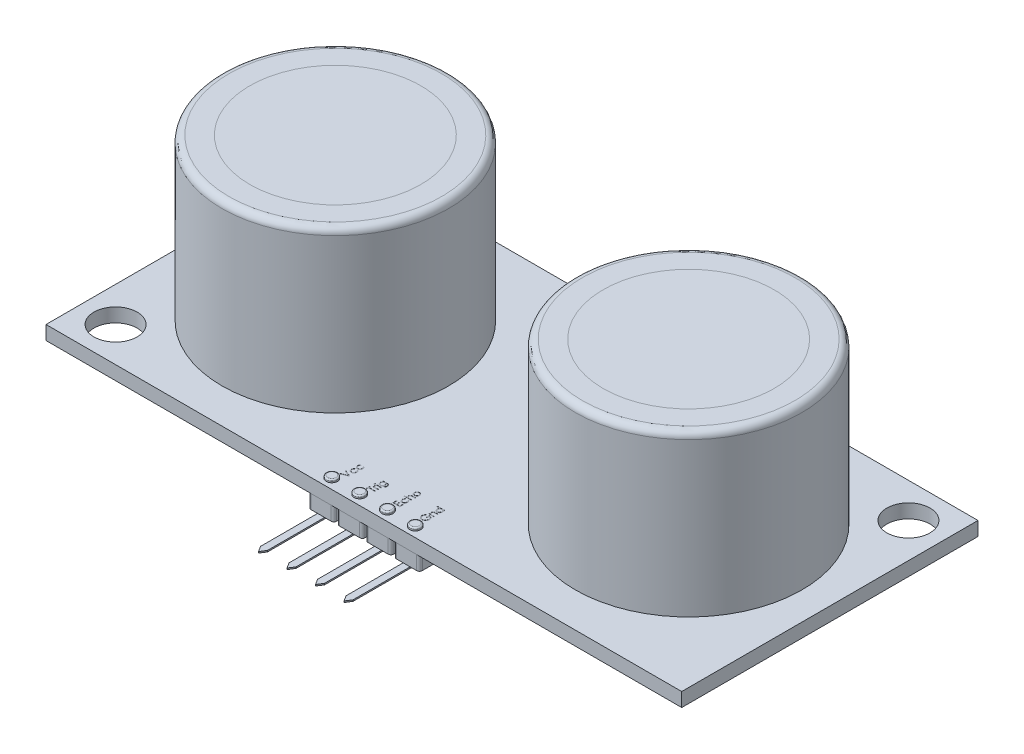
SolidWorks part; units mm, degrees
ref_plane "Front Plane" through (0, 0, 0) normal (0, 0, 1) x (1, 0, 0)
ref_plane "Top Plane" through (0, 0, 0) normal (0, 1, 0) x (1, 0, 0)
ref_plane "Right Plane" through (0, 0, 0) normal (1, 0, 0) x (0, 0, -1)
sketch "Sketch1" plane through (0, 0, 0) normal (0, 1, 0) x (1, 0, 0)
  line L1 (22.85, -10.65) -> (-22.85, -10.65)
  line L2 (22.85, -10.65) -> (22.85, 10.65)
  line L3 (22.85, 10.65) -> (-22.85, 10.65)
  line L4 (-22.85, -10.65) -> (-22.85, 10.65)
  line L5 (22.85, -10.65) -> (-22.85, 10.65) construction
  line L6 (22.85, 10.65) -> (-22.85, -10.65) construction
  circle A0 centre (20.35, 8.15) radius 1.55
  circle A1 centre (-20.35, -8.15) radius 1.55
  point P0 (0, 0)
  dimension "D3" = 3.1
  dimension "D1" = 45.7
  dimension "D2" = 21.3
  dimension "D4" = 2.5
  dimension "D5" = 2.5
  dimension "D6" = 2.5
  dimension "D7" = 2.5
extrude "Boss-Extrude1" add sketch "Sketch1" along normal blind 1
sketch "Sketch2" plane through (0, 1, 0) normal (0, 1, 0) x (1, 0, 0)
  line L0 (0, 0) -> (0, -50000) construction
  circle A0 centre (-12.7, 0) radius 8.15
  circle A1 centre (12.7, 0) radius 8.15
  circle A2 centre (-12.7, 0) radius 6.15
  circle A3 centre (12.7, 0) radius 6.15
  point P4 (20.85, 0)
  point P6 (-20.85, 0)
  dimension "D1" = 16.3
  dimension "D2" = 41.7
  dimension "D3" = 20.85
  dimension "D5" = 25.4
  dimension "D4" = 2
extrude "Boss-Extrude2" add sketch "Sketch2" along normal blind 11.54 separate body
fillet "Fillet1" radius 0.5 1 edges at (-12.7, 12.54, 8.15)
fillet "Fillet2" radius 0.5 1 edges at (12.7, 12.54, 8.15)
sketch "Sketch3" plane through (0, 1, 0) normal (0, 1, 0) x (1, 0, 0)
  circle A0 centre (-12.7, 0) radius 6
  circle A1 centre (12.7, 0) radius 6
  dimension "D1" = 12
extrude "Boss-Extrude3" add sketch "Sketch3" along normal blind 7 separate body
ref_plane "Plane1" through (12.7, 0, 0) normal (1, 0, 0) x (0, 0, -1)
sketch "Sketch5" plane through (12.7, 0, 0) normal (1, 0, 0) x (0, 0, -1)
  line L0 (0, 8) -> (0, -49992) construction
  line L1 (6, 8) -> (-6, 8) construction
  line L2 (0.75, 8.5) -> (0.75, 8.4)
  line L4 (0.75, 8.5) -> (0, 8.5)
  line L5 (4, 8.915) -> (2, 8)
  line L6 (0.75, 8.4) -> (0.95, 8.4)
  line L7 (0, 8.5) -> (0, 8)
  line L8 (0, 8) -> (2, 8)
  line L9 (0.95, 8.4) -> (4, 8.915)
  point P4 (0, 8)
  dimension "D1" = 4
  dimension "D2" = 0.5
  dimension "D3" = 0.75
  dimension "D4" = 0.1
  dimension "D5" = 2
  dimension "D6" = 15
  dimension "D7" = 0.2
revolve "Revolve1" add sketch "Sketch5" angle 360 about L0
pattern_linear "LPattern2" count 2 spacing 25.4 along (-1, 0, 0) of "Revolve1"
sketch "Sketch6" plane through (0, 12.54, 0) normal (0, 1, 0) x (1, 0, 0)
  circle A0 centre (-12.7, 0) radius 6.15
  circle A1 centre (12.7, 0) radius 6.15
  dimension "D1" = 12.3
extrude "Boss-Extrude4" add sketch "Sketch6" against normal blind 0.2 separate body
sketch "Sketch18" plane through (0, 0, 0) normal (0, -1, 0) x (1, 0, 0)
  line L0 (-22.85, 10.65) -> (22.85, 10.65) construction
  line L1 (-3.8, 10.65) -> (-2.35, 10.65)
  line L2 (-4, 10.45) -> (-4, 8.85)
  line L3 (-3.8, 8.65) -> (-2.35, 8.65)
  line L4 (4, 10.45) -> (4, 8.85)
  line L5 (0, 8.65) -> (0, 10.65) construction
  line L6 (-4, 9.65) -> (4, 9.65) construction
  line L7 (0, 0) -> (0, 50000) construction
  line L8 (-2.15, 10.45) -> (-2.15, 8.85)
  line L9 (0.1, 10.45) -> (0.1, 8.85)
  line L10 (-1.95, 10.45) -> (-1.95, 8.85)
  line L11 (-1.75, 10.65) -> (-0.3, 10.65)
  line L12 (-1.75, 8.65) -> (-0.3, 8.65)
  line L13 (-0.1, 8.85) -> (-0.1, 10.45)
  line L14 (0.3, 10.65) -> (1.75, 10.65)
  line L15 (0.3, 8.65) -> (1.75, 8.65)
  line L16 (1.95, 10.45) -> (1.95, 8.85)
  line L17 (2.15, 10.45) -> (2.15, 8.85)
  line L18 (2.35, 10.65) -> (3.8, 10.65)
  line L19 (2.35, 8.65) -> (3.8, 8.65)
  arc A0 (3.8, 8.65) -> (4, 8.85) centre (3.8, 8.85) ccw
  arc A1 (4, 10.45) -> (3.8, 10.65) centre (3.8, 10.45) ccw
  arc A2 (2.15, 8.85) -> (2.35, 8.65) centre (2.35, 8.85) ccw
  arc A3 (2.15, 10.45) -> (2.35, 10.65) centre (2.35, 10.45) cw
  arc A4 (1.95, 8.85) -> (1.75, 8.65) centre (1.75, 8.85) cw
  arc A5 (1.95, 10.45) -> (1.75, 10.65) centre (1.75, 10.45) ccw
  arc A6 (0.1, 8.85) -> (0.3, 8.65) centre (0.3, 8.85) ccw
  arc A7 (0.1, 10.45) -> (0.3, 10.65) centre (0.3, 10.45) cw
  arc A8 (-0.1, 8.85) -> (-0.3, 8.65) centre (-0.3, 8.85) cw
  arc A9 (-0.1, 10.45) -> (-0.3, 10.65) centre (-0.3, 10.45) ccw
  arc A10 (-1.95, 10.45) -> (-1.75, 10.65) centre (-1.75, 10.45) cw
  arc A11 (-1.95, 8.85) -> (-1.75, 8.65) centre (-1.75, 8.85) ccw
  arc A12 (-2.35, 8.65) -> (-2.15, 8.85) centre (-2.35, 8.85) ccw
  arc A13 (-2.15, 10.45) -> (-2.35, 10.65) centre (-2.35, 10.45) ccw
  arc A14 (-4, 8.85) -> (-3.8, 8.65) centre (-3.8, 8.85) ccw
  arc A15 (-4, 10.45) -> (-3.8, 10.65) centre (-3.8, 10.45) cw
  point P24 (4, 10.65)
  point P27 (2.15, 8.65)
  point P30 (2.15, 10.65)
  point P33 (1.95, 8.65)
  point P38 (0.1, 8.65)
  point P41 (0.1, 10.65)
  point P46 (-0.1, 10.65)
  point P49 (-1.95, 10.65)
  point P52 (-1.95, 8.65)
  point P59 (-4, 8.65)
  point P62 (-4, 10.65)
  point P212 (0, 9.65)
extrude "Boss-Extrude10" add sketch "Sketch18" along normal blind 1 separate body
sketch "Sketch13" plane through (0, 1, 0) normal (0, 1, 0) x (1, 0, 0)
  line L0 (-4, -10.65) -> (-4, -8.7338) construction
  line L1 (-22.85, -10.65) -> (22.85, -10.65) construction
  line L2 (-4, -8.7338) -> (4, -8.7338) construction
  line L3 (4, -8.7338) -> (4, -10.65) construction
  line L4 (4, -10.65) -> (-4, -10.65) construction
  line L5 (0, 0) -> (0, -50000) construction
  circle A0 centre (-3, -9.95) radius 0.4
  circle A1 centre (-1, -9.95) radius 0.4
  circle A2 centre (1, -9.95) radius 0.4
  circle A3 centre (3, -9.95) radius 0.4
  point P9 (-4, -9.6919)
extrude "Boss-Extrude8" add sketch "Sketch13" along normal blind 0.2 separate body
fillet "Fillet3" radius 0.1 1 edges at (-3, 1.2, 10.35)
fillet "Fillet4" radius 0.1 1 edges at (-1, 1.2, 10.35)
fillet "Fillet5" radius 0.1 1 edges at (1, 1.2, 10.35)
fillet "Fillet6" radius 0.1 1 edges at (3, 1.2, 10.35)
sketch "Sketch15" plane through (0, 1, 0) normal (0, 1, 0) x (1, 0, 0)
  line L0 (-22.85, -10.65) -> (22.85, -10.65) construction
  line L1 (3.4865, -7.65) -> (-2.4849, -7.65) construction
  line L2 (3.4865, -7.65) -> (3.4865, -10.65) construction
  line L3 (3.4865, -10.65) -> (-2.4849, -10.65) construction
  line L5 (-2.4849, -7.65) -> (-2.4849, -10.65) construction
  line L6 (3.4865, -7.65) -> (-2.4849, -10.65) construction
  line L7 (3.4865, -10.65) -> (-2.4849, -7.65) construction
  text T0 "Vcc  \r\nTrig   \r\nEcho\r\nGnd " font "Century Gothic" height 0.5
  point P0 (0.5008, -9.15)
  dimension "D1" = 3
extrude "Cut-Extrude5" cut sketch "Sketch15" against normal blind 0.01
sketch "Sketch19" plane through (0, -1, 0) normal (0, -1, 0) x (1, 0, 0)
  line L1 (3.325, 9.15) -> (2.825, 9.15)
  line L2 (3.325, 9.15) -> (3.325, 14.75)
  line L3 (3.075, 15.15) -> (2.825, 15.15)
  line L4 (2.825, 9.15) -> (2.825, 14.75)
  line L5 (3.075, 15.15) -> (3.075, 9.15) construction
  line L6 (3.325, 12.15) -> (2.825, 12.15) construction
  line L7 (1.275, 9.15) -> (0.775, 9.15)
  line L8 (1.275, 9.15) -> (1.275, 14.75)
  line L9 (1.025, 15.15) -> (0.775, 15.15)
  line L10 (0.775, 9.15) -> (0.775, 14.75)
  line L11 (1.025, 15.15) -> (1.025, 9.15) construction
  line L12 (1.275, 12.15) -> (0.775, 12.15) construction
  line L13 (-0.775, 9.15) -> (-1.275, 9.15)
  line L14 (-0.775, 9.15) -> (-0.775, 14.75)
  line L15 (-1.025, 15.15) -> (-1.275, 15.15)
  line L16 (-1.275, 9.15) -> (-1.275, 14.75)
  line L17 (-1.025, 15.15) -> (-1.025, 9.15) construction
  line L18 (-0.775, 12.15) -> (-1.275, 12.15) construction
  line L19 (-2.825, 9.15) -> (-3.325, 9.15)
  line L20 (-2.825, 9.15) -> (-2.825, 14.75)
  line L21 (-3.075, 15.15) -> (-3.325, 15.15)
  line L22 (-3.325, 9.15) -> (-3.325, 14.75)
  line L23 (-3.075, 15.15) -> (-3.075, 9.15) construction
  line L24 (-2.825, 12.15) -> (-3.325, 12.15) construction
  line L26 (-1.75, 8.65) -> (-0.3, 8.65) construction
  line L27 (-3.8, 8.65) -> (-2.35, 8.65) construction
  line L29 (-3.075, 15.15) -> (-2.825, 14.75)
  line L30 (-3.075, 15.15) -> (-3.325, 14.75)
  line L31 (-1.025, 15.15) -> (-0.775, 14.75)
  line L32 (1.025, 15.15) -> (1.275, 14.75)
  line L33 (-1.275, 14.75) -> (-1.025, 15.15)
  line L34 (1.025, 15.15) -> (0.775, 14.75)
  line L35 (3.075, 15.15) -> (3.325, 14.75)
  line L37 (2.825, 14.75) -> (3.075, 15.15)
  point P20 (-1.025, 8.65)
  point P23 (-3.075, 8.65)
  point P300 (-1.025, 12.15)
  point P301 (-3.075, 12.15)
  point P352 (1.025, 12.15)
  point P420 (3.075, 12.15)
  dimension "D2" = 6
  dimension "D3" = 0.5
  dimension "D4" = 0.5
  dimension "D5" = 0.5
  dimension "D6" = 0.5
  dimension "D7" = 0.4
  dimension "D8" = 0.4
  dimension "D9" = 0.4717
extrude "Boss-Extrude11" add sketch "Sketch19" along normal blind 0.1 separate body contours L29 L20 L19 L22 L30 | L31 L14 L13 L16 L33 | L32 L8 L7 L10 L34 | L35 L2 L1 L4 L37
sketch "Sketch21" plane through (0, 1, 0) normal (0, 1, 0) x (1, 0, 0)
  line L0 (22.85, 10.65) -> (-22.85, 10.65) construction
  line L1 (3, 6.65) -> (-3, 6.65)
  line L3 (3, 9.65) -> (-3, 9.65)
  arc A0 (-3, 9.65) -> (-3, 6.65) centre (-3, 8.15) ccw
  arc A1 (3, 6.65) -> (3, 9.65) centre (3, 8.15) ccw
  point P14 (-4.5, 8.15)
  point P16 (4.5, 8.15)
  dimension "D1" = 3
  dimension "D2" = 6
  dimension "D3" = 1
extrude "Boss-Extrude13" add sketch "Sketch21" along normal blind 0.5 separate body
sketch "Sketch22" plane through (0, 1.5, 0) normal (0, 1, 0) x (1, 0, 0)
  line L1 (-2.9874, 7.15) -> (3, 7.15)
  line L3 (-3, 9.15) -> (3, 9.15)
  line L4 (-3, 6.65) -> (3, 6.65) construction
  arc A0 (-3, 9.15) -> (-2.9874, 7.15) centre (-3, 8.15) ccw
  arc A1 (3, 7.15) -> (3, 9.15) centre (3, 8.15) ccw
  arc A2 (-3, 9.65) -> (-3, 6.65) centre (-3, 8.15) ccw construction
  arc A3 (3, 6.65) -> (3, 9.65) centre (3, 8.15) ccw construction
  point P2 (4.5, 8.15)
  point P3 (4, 8.15)
  point P4 (-4.5, 8.15)
  point P5 (-4, 8.1437)
  dimension "D1" = 0.5
  dimension "D3" = 1
  dimension "D2" = 2
  dimension "D4" = 0.5
  dimension "D5" = 0.5
extrude "Boss-Extrude14" add sketch "Sketch22" along normal blind 1.5
fillet "Fillet7" radius 0.1 8 edges at (-4, 3, -8.1437) (0, 3, -9.15) (4, 3, -8.15) (-4.5, 1.5, -8.15) (0, 1.5, -9.65) (4.5, 1.5, -8.15) (0.0063, 3, -7.15) (0, 1.5, -6.65)
equation "\"D2@Sketch13\"=\"D1@Sketch13\"/2"
equation "\"D9@Sketch18\"=\"D1@Sketch18\"/2"
